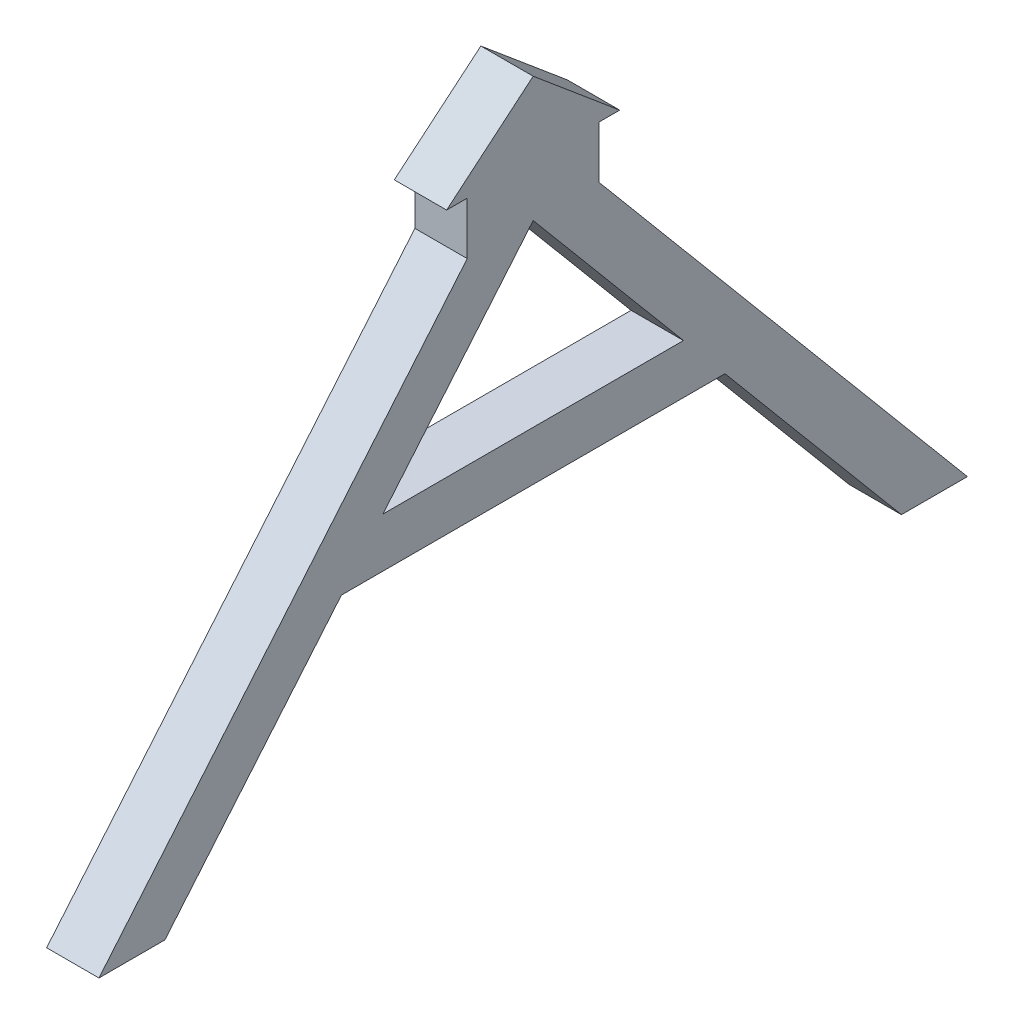
SolidWorks part; units mm, degrees
ref_plane "Front Plane" through (0, 0, 0) normal (0, 0, 1) x (1, 0, 0)
ref_plane "Top Plane" through (0, 0, 0) normal (0, 1, 0) x (1, 0, 0)
ref_plane "Right Plane" through (0, 0, 0) normal (1, 0, 0) x (0, 0, -1)
sketch "Sketch1" plane through (0, 0, 0) normal (1, 0, 0) x (0, 0, -1)
  line L5 (0, 0) -> (1.25, 0)
  line L6 (10.5, 0) -> (5.25, 4.4053)
  line L7 (5.25, 4.4053) -> (0, 0)
  line L8 (9.25, 0) -> (10.5, 0)
  line L10 (1.25, 0) -> (1.25, -3.175)
  line L12 (9.25, 0) -> (9.25, -3.175)
  line L13 (1.25, -3.175) -> (-21.0878, -29.7961)
  line L14 (-21.0878, -29.7961) -> (-17.0878, -29.7961)
  line L15 (-17.0878, -29.7961) -> (-6.3819, -17.0374)
  line L16 (5.25, -3.175) -> (14.3646, -14.0374)
  line L17 (27.5878, -29.7961) -> (31.5878, -29.7961)
  line L18 (31.5878, -29.7961) -> (9.25, -3.175)
  line L19 (-3.8646, -14.0374) -> (14.3646, -14.0374)
  line L20 (-6.3819, -17.0374) -> (16.8819, -17.0374)
  line L21 (16.8819, -17.0374) -> (27.5878, -29.7961)
  line L22 (-3.8646, -14.0374) -> (5.25, -3.175)
  line L23 (1.25, -3.175) -> (5.25, -3.175) construction
  line L24 (5.25, -3.175) -> (9.25, -3.175) construction
  dimension "D1" = 10.5
  dimension "D2" = 8
  dimension "D3" = 3.175
  dimension "D4" = 80
  dimension "D5" = 4
  dimension "D6" = 3
  dimension "D7" = 40
extrude "Boss-Extrude2" add sketch "Sketch1" along normal blind 3.175 contours L22 L16 L19
